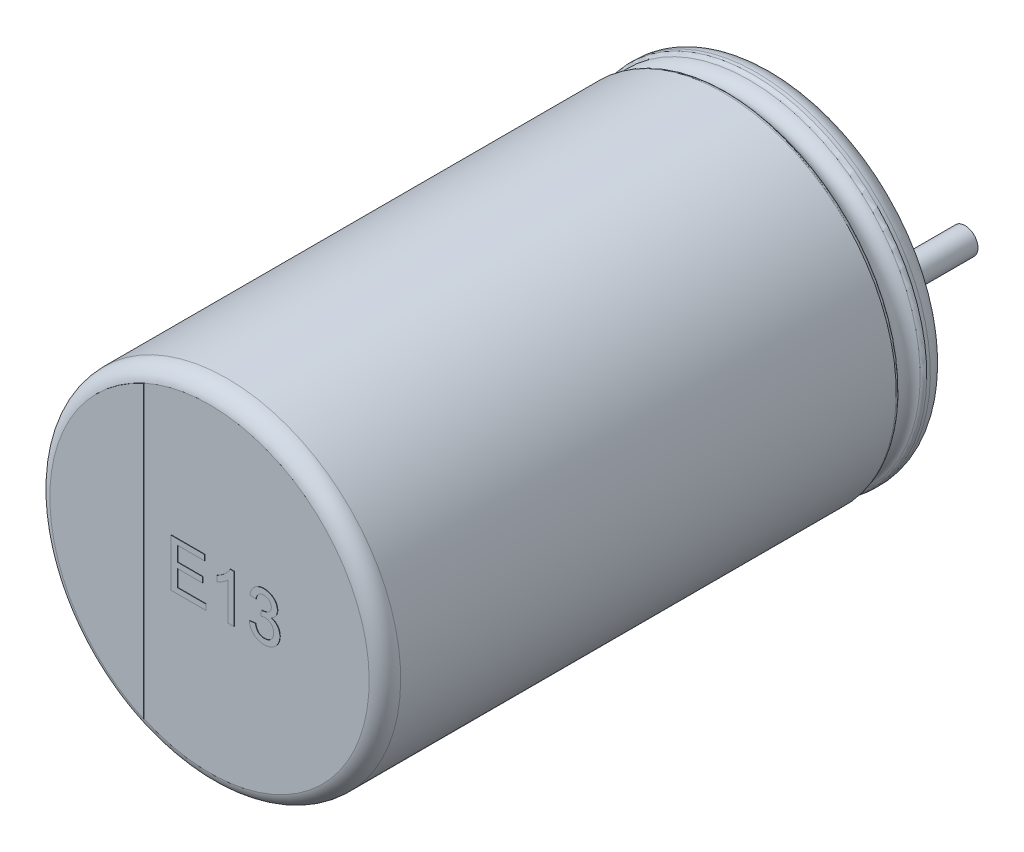
SolidWorks part; units mm, degrees
ref_plane "Plan de face" through (0, 0, 0) normal (0, 0, 1) x (1, 0, 0)
ref_plane "Plan de dessus" through (0, 0, 0) normal (0, 1, 0) x (1, 0, 0)
ref_plane "Plan de droite" through (0, 0, 0) normal (1, 0, 0) x (0, 0, -1)
sketch "Sketch10" plane through (0, 0, 0) normal (1, 0, 0) x (0, 0, -1)
  line L0 (18.1631, 0) -> (-18.9631, 0) construction
  line L1 (-13, 0) -> (-0.05, 0)
  line L2 (-13, 0) -> (-13, 3.6736)
  line L3 (-12.6, 4) -> (-1.1846, 4)
  line L4 (-0.05, 3.4031) -> (-0.05, 0)
  line L7 (-0.4794, 4) -> (-0.3982, 4)
  arc A0 (-13, 3.6736) -> (-12.6, 4) centre (-12.6068, 3.6001) cw
  arc A1 (-0.3982, 4) -> (-0.05, 3.4031) centre (-0.3982, 3.6) cw
  arc A2 (-0.5713, 3.9394) -> (-1.0926, 3.9394) centre (-0.832, 4.051) cw
  arc A3 (-1.0926, 3.9394) -> (-1.1846, 4) centre (-1.1846, 3.9) ccw
  arc A4 (-0.5713, 3.9394) -> (-0.4794, 4) centre (-0.4794, 3.9) cw
  point P4 (0.57, 0)
  point P13 (-13, 4)
  dimension "D2" = 0.4
  dimension "D3" = 0.4
  dimension "D4" = 0.1
  dimension "D5" = 0.1
  dimension "D1" = 4
revolve "Повернуть1" add sketch "Sketch10" angle 360 about L0
sketch "Эскиз2" plane through (0, 0, 0.05) normal (0, 0, -1) x (-1, 0, 0)
  line L1 (0, 0.7993) -> (0, -1.0496) construction
  line L2 (-1.75, 0) -> (3.1313, 0) construction
  circle A3 centre (-1.75, 0) radius 0.3
  circle A7 centre (1.75, 0) radius 0.3
  dimension "D1" = 3.5
extrude "Бобышка-Вытянуть1" add sketch "Эскиз2" along normal blind 2.7
sketch "Эскиз4" plane through (0, 0, 13) normal (0, 0, 1) x (1, 0, 0)
  line L0 (-1.5096, -3.3491) -> (-1.5096, 3.3491)
  circle A1 centre (0, 0) radius 3.6736 construction
  arc A2 (-1.5096, 3.3491) -> (-1.5096, -3.3491) centre (0, 0) ccw
extrude "Бобышка-Вытянуть2" add sketch "Эскиз4" along normal blind 0.01
sketch "Эскиз5" plane through (0, 0, 13) normal (0, 0, 1) x (1, 0, 0)
  text T0 "E13" font "Arial" height 1.1
extrude "Текст" add sketch "Эскиз5" along normal blind 0.01
sketch "Эскиз6" plane through (0, 0, 0.05) normal (0, 0, -1) x (-1, 0, 0)
  line L0 (-1.75, 0.4656) -> (-2.1332, 0.4656)
  line L1 (-1.75, -0.4656) -> (-2.1332, -0.4656)
  line L2 (1.75, -0.4656) -> (2.1332, -0.4656)
  line L3 (1.75, 0.4656) -> (2.1332, 0.4656)
  arc A0 (-2.3702, -0.7952) -> (2.3702, -0.7952) centre (0, 0) ccw
  arc A1 (-1.75, -0.4656) -> (-1.75, 0.4656) centre (-1.75, 0) ccw
  arc A2 (1.75, 0.4656) -> (1.75, -0.4656) centre (1.75, 0) ccw
  arc A3 (2.3702, 0.7952) -> (-2.3702, 0.7952) centre (0, 0) ccw
  arc A4 (2.1332, 0.4656) -> (2.3702, 0.7952) centre (2.1332, 0.7156) ccw
  arc A5 (2.1332, -0.4656) -> (2.3702, -0.7952) centre (2.1332, -0.7156) cw
  arc A6 (-2.3702, -0.7952) -> (-2.1332, -0.4656) centre (-2.1332, -0.7156) cw
  arc A7 (-2.1332, 0.4656) -> (-2.3702, 0.7952) centre (-2.1332, 0.7156) cw
  point P7 (2.4563, 0.4656)
  point P23 (0, -2.5)
  point P24 (0, 2.5)
  dimension "D1" = 0.25
  dimension "D2" = 5
extrude "Бобышка-Вытянуть5" add sketch "Эскиз6" along normal blind 0.05 contours A3 A7 L0 A1 L1 A6 A0 A5 L2 A2 L3 A4
